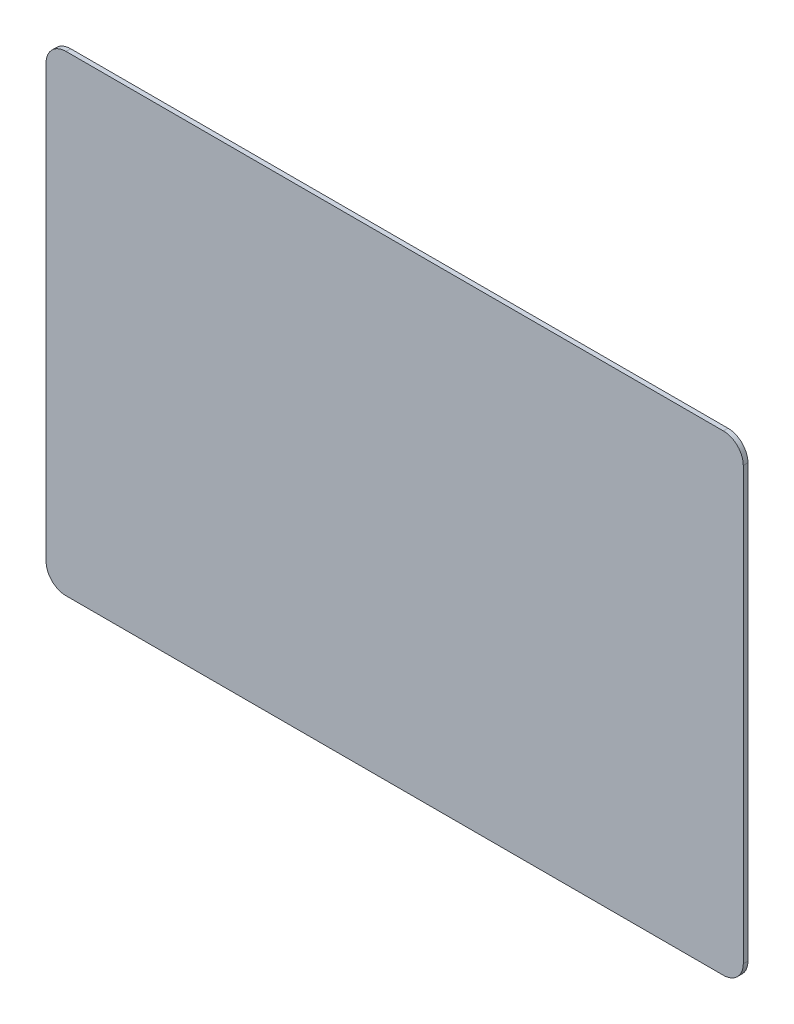
SolidWorks part; units mm, degrees
ref_plane "Front Plane" through (0, 0, 0) normal (0, 0, 1) x (1, 0, 0)
ref_plane "Top Plane" through (0, 0, 0) normal (0, 1, 0) x (1, 0, 0)
ref_plane "Right Plane" through (0, 0, 0) normal (1, 0, 0) x (0, 0, -1)
sketch "Sketch1" plane through (0, 0, 0) normal (0, 0, 1) x (1, 0, 0)
  line L4 (52.5, -272.0918) -> (52.5, -207.0918)
  line L5 (49.5, -204.0918) -> (-49.5, -204.0918)
  line L6 (-52.5, -207.0918) -> (-52.5, -272.0918)
  line L7 (-49.5, -275.0918) -> (49.5, -275.0918)
  line L8 (52.5, -272.0918) -> (52.5, -207.0918)
  line L9 (49.5, -204.0918) -> (-49.5, -204.0918)
  line L10 (-52.5, -207.0918) -> (-52.5, -272.0918)
  line L11 (-49.5, -275.0918) -> (49.5, -275.0918)
  arc A4 (49.5, -275.0918) -> (52.5, -272.0918) centre (49.5, -272.0918) ccw
  arc A5 (52.5, -207.0918) -> (49.5, -204.0918) centre (49.5, -207.0918) ccw
  arc A6 (-49.5, -204.0918) -> (-52.5, -207.0918) centre (-49.5, -207.0918) ccw
  arc A7 (-52.5, -272.0918) -> (-49.5, -275.0918) centre (-49.5, -272.0918) ccw
  arc A8 (49.5, -275.0918) -> (52.5, -272.0918) centre (49.5, -272.0918) ccw
  arc A9 (52.5, -207.0918) -> (49.5, -204.0918) centre (49.5, -207.0918) ccw
  arc A10 (-49.5, -204.0918) -> (-52.5, -207.0918) centre (-49.5, -207.0918) ccw
  arc A11 (-52.5, -272.0918) -> (-49.5, -275.0918) centre (-49.5, -272.0918) ccw
  dimension "D1" = 0
extrude "Boss-Extrude1" add sketch "Sketch1" against normal up to surface (0.7 mm away)
